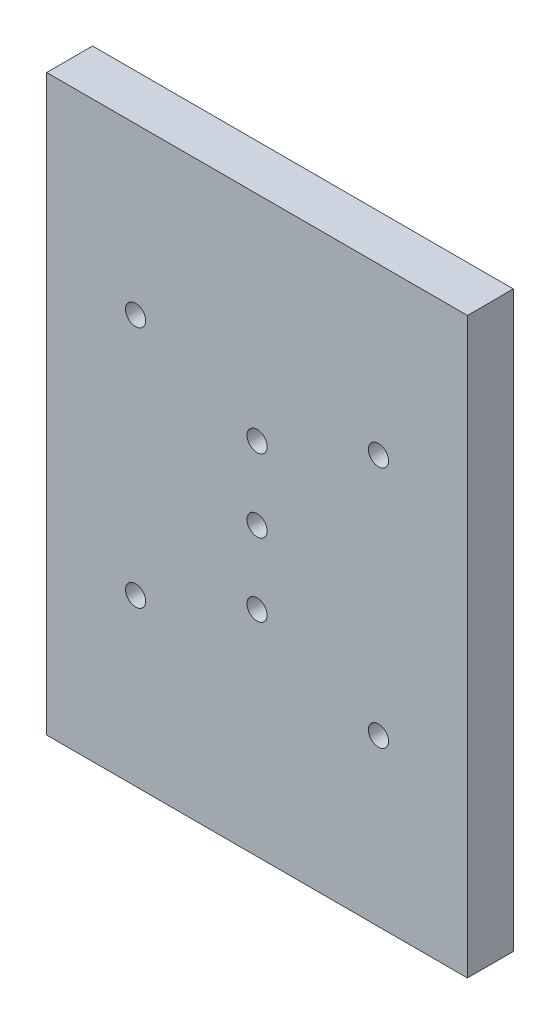
SolidWorks part; units mm, degrees
ref_plane "Front Plane" through (0, 0, 0) normal (0, 0, 1) x (1, 0, 0)
ref_plane "Top Plane" through (0, 0, 0) normal (0, 1, 0) x (1, 0, 0)
ref_plane "Right Plane" through (0, 0, 0) normal (1, 0, 0) x (0, 0, -1)
sketch "Sketch1" plane through (0, 0, 0) normal (0, 0, 1) x (1, 0, 0)
  line L0 (-55, 0) -> (0, -75) construction
  line L1 (0, 0) -> (-55, 0)
  line L2 (0, 0) -> (0, -75)
  line L3 (0, -75) -> (-55, -75)
  line L4 (-55, 0) -> (-55, -75)
  line L5 (0, 0) -> (-55, -75) construction
  line L6 (-27.5, -37.5) -> (-27.5, -26.0057) construction
  line L7 (-43.375, -21.625) -> (-11.625, -21.625) construction
  line L8 (-11.625, -21.625) -> (-11.625, -53.375) construction
  line L9 (-11.625, -53.375) -> (-43.375, -53.375) construction
  line L10 (-43.375, -53.375) -> (-43.375, -21.625) construction
  line L11 (-43.375, -21.625) -> (-11.625, -53.375) construction
  line L12 (-11.625, -53.375) -> (-27.5, -37.5) construction
  line L13 (-27.5, -27.97) -> (-27.5, -47.03) construction
  circle A0 centre (-43.375, -21.625) radius 1.32
  circle A1 centre (-11.625, -21.625) radius 1.32
  circle A2 centre (-11.625, -53.375) radius 1.32
  circle A3 centre (-43.375, -53.375) radius 1.32
  circle A4 centre (-27.5, -27.97) radius 1.32
  circle A5 centre (-27.5, -37.5) radius 1.32
  circle A6 centre (-27.5, -47.03) radius 1.32
  dimension "D3" = 2.64
  dimension "D8" = 2.64
  dimension "D9" = 3
  dimension "D10" = 9.53
  dimension "D1" = 55
  dimension "D2" = 75
  dimension "D6" = 31.75
  dimension "D7" = 31.75
  dimension "D4" = 2
  dimension "D5" = 2
extrude "Boss-Extrude1" add sketch "Sketch1" along normal blind 6
sketch "Sketch2" plane through (0, 0, 0) normal (0, 0, -1) x (-1, 0, 0)
  circle A0 centre (11.625, -21.625) radius 3.25
  circle A1 centre (43.375, -21.625) radius 3.25
  circle A2 centre (43.375, -53.375) radius 3.25
  circle A3 centre (11.625, -53.375) radius 3.25
  dimension "D1" = 6.5
  dimension "D2" = 2
  dimension "D3" = 2
extrude "Cut-Extrude1" cut sketch "Sketch2" against normal blind 4
